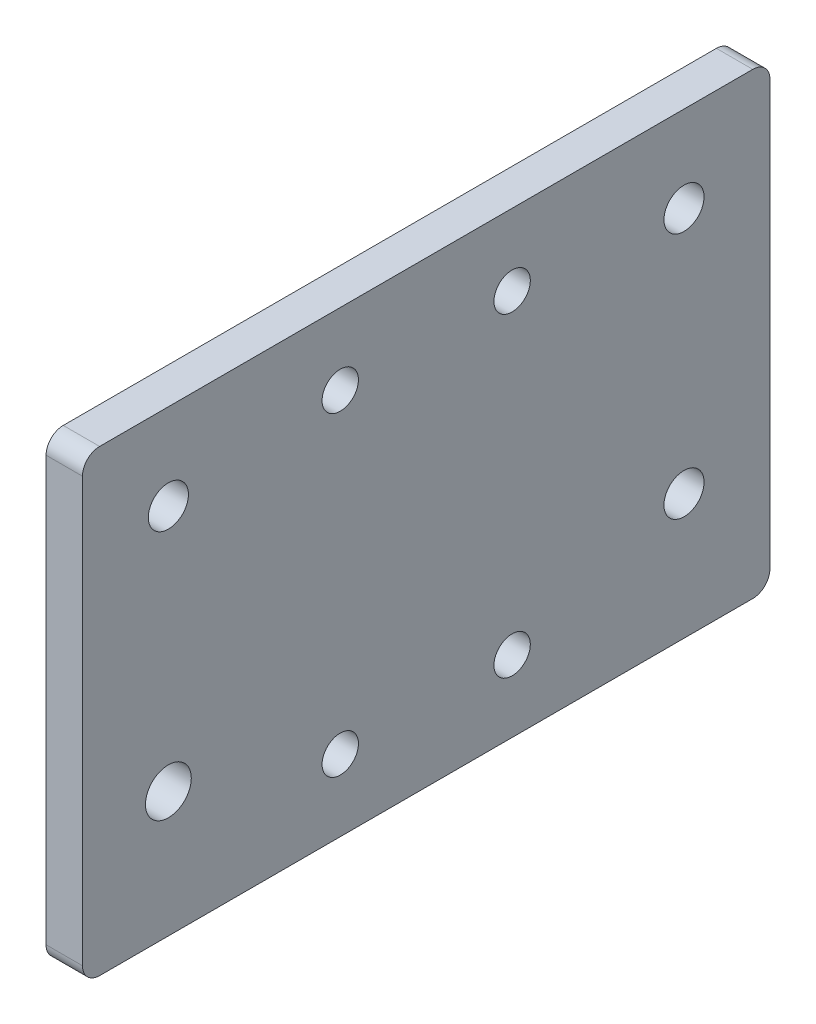
SolidWorks part; units mm, degrees
ref_plane "Front Plane" through (0, 0, 0) normal (0, 0, 1) x (1, 0, 0)
ref_plane "Top Plane" through (0, 0, 0) normal (0, 1, 0) x (1, 0, 0)
ref_plane "Right Plane" through (0, 0, 0) normal (1, 0, 0) x (0, 0, -1)
sketch "Sketch1" plane through (0, 0, 0) normal (1, 0, 0) x (0, 0, -1)
  line L0 (0, 40) -> (0, -40) construction
  line L1 (-60, -40) -> (60, -40)
  line L2 (-60, -40) -> (-60, 40)
  line L3 (-60, 40) -> (60, 40)
  line L4 (60, -40) -> (60, 40)
  line L5 (-60, -40) -> (60, 40) construction
  line L6 (-60, 40) -> (60, -40) construction
  line L7 (-60, -18.13) -> (60, -18.13) construction
  line L8 (-45, 25) -> (-45, -18.13) construction
  line L9 (45, 25) -> (45, -18.13) construction
  circle A0 centre (-45, 25) radius 15 construction
  circle A1 centre (45, 25) radius 15 construction
  circle A2 centre (45, 25) radius 3.5
  circle A3 centre (-45, 25) radius 3.5
  circle A4 centre (-45, -18.13) radius 4
  circle A5 centre (45, -18.13) radius 3.5
  point P0 (0, 0)
  dimension "D3" = 30
  dimension "D4" = 7
  dimension "D5" = 7
  dimension "D7" = 8
  dimension "D8" = 7
  dimension "D1" = 120
  dimension "D2" = 80
  dimension "D6" = 43.13
extrude "Boss-Extrude1" add sketch "Sketch1" along normal blind 6.35 contours L2 L1 L4 L3 | A5
fillet "Fillet1" radius 3 4 edges at (3.175, -40, -60) (3.175, -40, 60) (3.175, 40, 60) (3.175, 40, -60)
sketch "Sketch2" plane through (6.35, 0, 0) normal (1, 0, 0) x (0, 0, -1)
  line L0 (0, 40) -> (0, -40) construction
  line L1 (57, 40) -> (-57, 40) construction
  line L2 (-57, -40) -> (57, -40) construction
  line L4 (-15, 27.5) -> (15, 27.5) construction
  line L5 (-15, 27.5) -> (-15, -27.5) construction
  line L6 (-15, -27.5) -> (15, -27.5) construction
  line L7 (15, 27.5) -> (15, -27.5) construction
  line L8 (-15, 27.5) -> (15, -27.5) construction
  line L9 (-15, -27.5) -> (15, 27.5) construction
  circle A0 centre (-15, 27.5) radius 3.175
  circle A1 centre (15, 27.5) radius 3.175
  circle A2 centre (15, -27.5) radius 3.175
  circle A3 centre (-15, -27.5) radius 3.175
  point P6 (0, 0)
  dimension "D3" = 6.35
  dimension "D1" = 30
  dimension "D2" = 55
extrude "Cut-Extrude1" cut sketch "Sketch2" against normal blind 10
